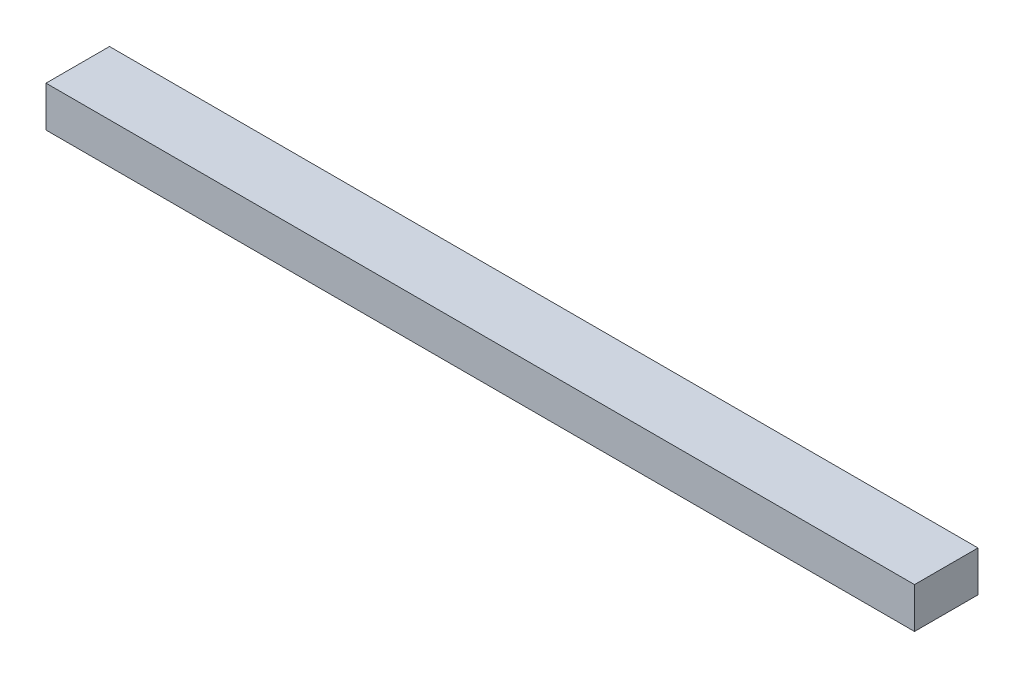
SolidWorks part; units mm, degrees
ref_plane "Plan de face" through (0, 0, 0) normal (0, 0, 1) x (1, 0, 0)
ref_plane "Plan de dessus" through (0, 0, 0) normal (0, 1, 0) x (1, 0, 0)
ref_plane "Plan de droite" through (0, 0, 0) normal (1, 0, 0) x (0, 0, -1)
sketch "Esquisse1" plane through (0, 0, 0) normal (0, 0, 1) x (1, 0, 0)
  line L1 (201, -193) -> (-141, -193)
  line L2 (201, -193) -> (201, -177)
  line L3 (201, -177) -> (-141, -177)
  line L4 (-141, -193) -> (-141, -177)
  dimension "D1" = 16
extrude "Boss.-Extru.1" add sketch "Esquisse1" along normal blind 25
